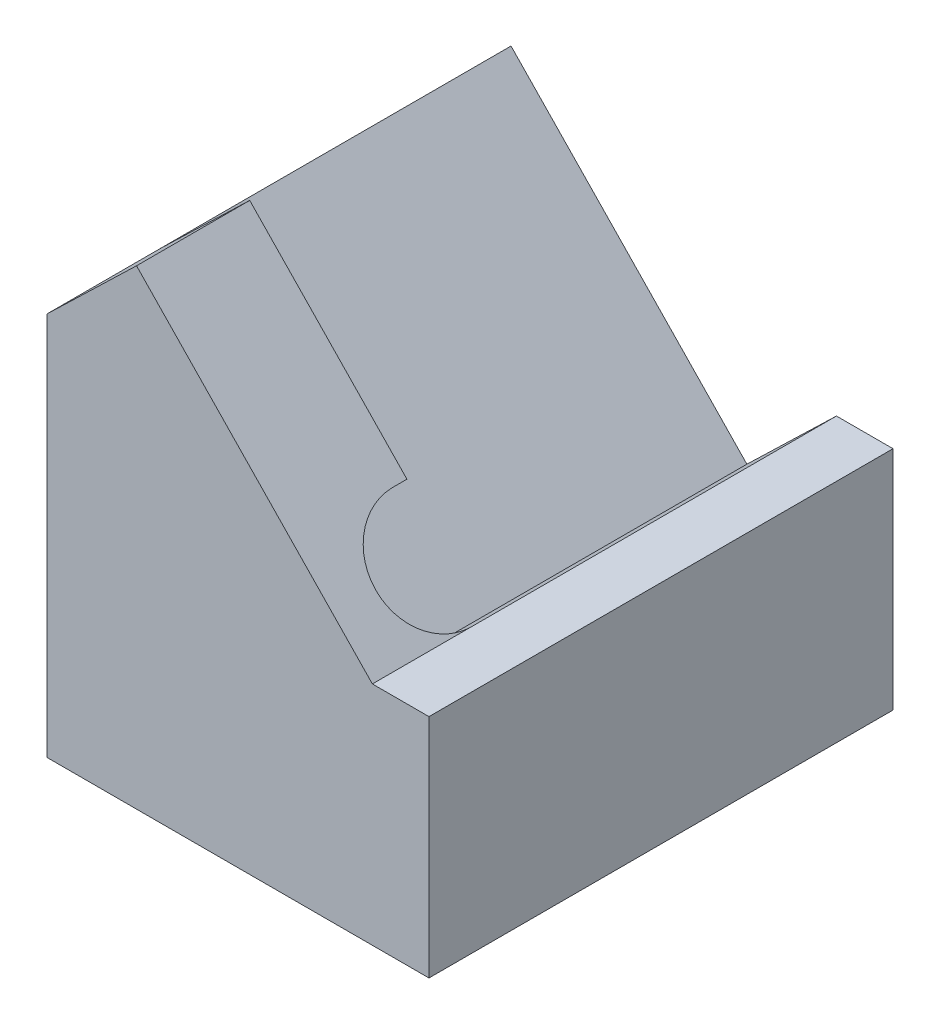
SolidWorks part; units mm, degrees
ref_plane "Front Plane" through (0, 0, 0) normal (0, 0, 1) x (1, 0, 0)
ref_plane "Top Plane" through (0, 0, 0) normal (0, 1, 0) x (1, 0, 0)
ref_plane "Right Plane" through (0, 0, 0) normal (1, 0, 0) x (0, 0, -1)
sketch "Sketch1" plane through (0, 0, 0) normal (0, 0, 1) x (1, 0, 0)
  line L0 (0, 0) -> (0, 4.7873)
  line L1 (0, 4.7873) -> (1.5825, 6.3155)
  line L2 (1.5825, 6.3155) -> (5.75, 2)
  line L3 (5.75, 2) -> (6.75, 2)
  line L4 (6.75, 2) -> (6.75, 0)
  line L5 (6.75, 0) -> (0, 0)
  dimension "D1" = 2
  dimension "D2" = 1
  dimension "D3" = 134
  dimension "D4" = 2.2
  dimension "D5" = 6.75
extrude "Boss-Extrude1" add sketch "Sketch1" along normal blind 8.2
sketch "Sketch2" plane through (3.9747, 3.8383, 0) normal (0.7193, 0.6947, 0) x (0, 0, -1)
  line L0 (0, 3.4437) -> (0, -2.5556)
  line L1 (0, -2.5556) -> (-6.45, -2.5556)
  line L2 (-8.2, -2.5556) -> (0, -2.5556) construction
  line L3 (-6.45, -0.5556) -> (-6.2, -0.5556)
  line L4 (-6.2, -0.5556) -> (-6.2, 3.4437)
  line L5 (-8.2, 3.4437) -> (0, 3.4437) construction
  line L6 (-6.2, 3.4437) -> (0, 3.4437)
  arc A0 (-6.45, -2.5556) -> (-6.45, -0.5556) centre (-6.45, -1.5556) cw
  dimension "D1" = 6.2
  dimension "D2" = 2
  dimension "D3" = 0.25
extrude "Cut-Extrude1" cut sketch "Sketch2" against normal blind 2.2
sketch "Sketch3" plane through (0, 0, 0) normal (0, -1, 0) x (1, 0, 0)
  line L1 (0, 0) -> (6.75, 0)
  line L2 (0, 0) -> (0, 8.2)
  line L3 (0, 8.2) -> (6.75, 8.2)
  line L4 (6.75, 0) -> (6.75, 8.2)
extrude "Boss-Extrude2" add sketch "Sketch3" along normal blind 2
hole_wizard "Ø1.5mm Dowel Hole1" positions "Sketch5" profile "Sketch4" hole size "Ø1.5" standard "ISO"
sketch "Sketch5" plane through (0, -2, 0) normal (0, -1, 0) x (-1, 0, 0)
  line L0 (0, -8.2) -> (0, 0) construction
  point P0 (-2, -7.1)
  point P2 (-2, -1.1)
  point P5 (0, -4.1)
  dimension "D1" = 6
  dimension "D2" = 3
  dimension "D3" = 2
sketch "Sketch4" plane through (2, -2, 7.1) normal (1, 0, 0) x (0, 0, -1)
  line L0 (0, 0) -> (0, 3.4506)
  line L1 (0, 3.4506) -> (0.75, 3)
  line L2 (0.75, 3) -> (0.75, 0)
  line L5 (0.75, 0) -> (0, 0)
  line L10 (0, 3.4506) -> (-0.75, 3) construction
  line L11 (0, -6.35) -> (0, 107.95) construction
  dimension "Hole Dia." = 1.5
  dimension "Hole Depth" = 3
  dimension "Drill Angle" = 118
hole_wizard "M2x0.4 Tapped Hole1" positions "Sketch7" profile "Sketch6" tap size "M2x0.4" standard "ANSI Metric"
sketch "Sketch7" plane through (0, -2, 0) normal (0, -1, 0) x (-1, 0, 0)
  line L0 (0, -8.2) -> (0, 0) construction
  line L1 (0, 0) -> (-6.75, 0) construction
  point P0 (-2, -4.1)
  dimension "D1" = 2
  dimension "D2" = 4.1
sketch "Sketch6" plane through (2, -2, 4.1) normal (1, 0, 0) x (0, 0, -1)
  line L0 (0, 0) -> (0, 3.4807)
  line L1 (0, 3.4807) -> (0.8, 3)
  line L2 (0.8, 3) -> (0.8, 0)
  line L5 (0.8, 0) -> (0, 0)
  line L10 (0, 3.4807) -> (-0.8, 3) construction
  line L11 (0, -6.35) -> (0, 107.95) construction
  dimension "Tap Drill Dia." = 1.6
  dimension "Tap Drill Depth" = 3
  dimension "Drill Angle" = 118
cosmetic thread "Hole Thread1" parameters "D1"=2.5, "D2"=2
